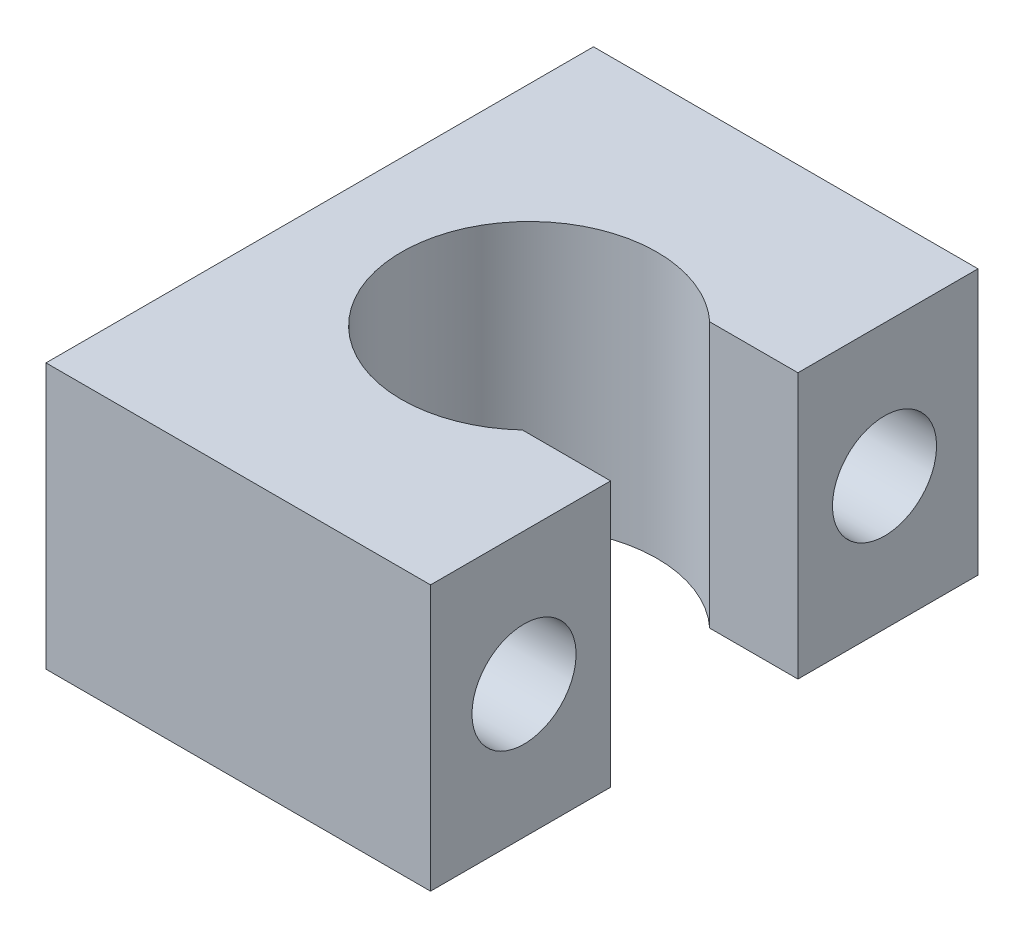
SolidWorks part; units mm, degrees
ref_plane "Front Plane" through (0, 0, 0) normal (0, 0, 1) x (1, 0, 0)
ref_plane "Top Plane" through (0, 0, 0) normal (0, 1, 0) x (1, 0, 0)
ref_plane "Right Plane" through (0, 0, 0) normal (1, 0, 0) x (0, 0, -1)
sketch "Sketch1" plane through (0, 0, 0) normal (0, 1, 0) x (1, 0, 0)
  line L5 (10.16, -14.465) -> (-10.16, -14.465)
  line L6 (10.16, -14.465) -> (10.16, 14.465)
  line L7 (10.16, 14.465) -> (-10.16, 14.465)
  line L8 (-10.16, -14.465) -> (-10.16, 14.465)
  line L9 (10.16, -14.465) -> (-10.16, 14.465) construction
  line L10 (10.16, 14.465) -> (-10.16, -14.465) construction
  point P0 (0, 0)
  dimension "D1" = 28.93
  dimension "D2" = 20.32
extrude "Boss-Extrude1" add sketch "Sketch1" along normal blind 14.02
sketch "Sketch2" plane through (0, 14.02, 0) normal (0, 1, 0) x (1, 0, 0)
  line L0 (10.16, -14.465) -> (10.16, 14.465) construction
  line L1 (10.16, -4.95) -> (5.4991, -4.95)
  line L2 (10.16, 4.95) -> (5.4991, 4.95)
  line L3 (10.16, -4.95) -> (10.16, 4.95) construction
  line L4 (10.16, -4.95) -> (10.16, 4.95)
  arc A0 (5.4991, 4.95) -> (5.4991, -4.95) centre (0.91, 0) ccw
  point P9 (10.16, 0)
  dimension "D1" = 13.5
  dimension "D2" = 9.25
  dimension "D3" = 9.9
extrude "Cut-Extrude1" cut sketch "Sketch2" against normal through all
sketch "Sketch3" plane through (-10.16, 0, 0) normal (-1, 0, 0) x (0, 0, 1)
  line L0 (9.525, 7.01) -> (-9.525, 7.01) construction
  line L1 (14.465, 14.02) -> (14.465, 0) construction
  circle A0 centre (9.525, 7.01) radius 2.75
  circle A1 centre (-9.525, 7.01) radius 2.75
  point P4 (0, 7.01)
  point P8 (14.465, 7.01)
  dimension "D1" = 5.5
  dimension "D2" = 19.05
extrude "Cut-Extrude2" cut sketch "Sketch3" against normal through all
ref_plane "Plane1" through (0, 7.01, 0) normal (0, -1, 0) x (-1, 0, 0)
